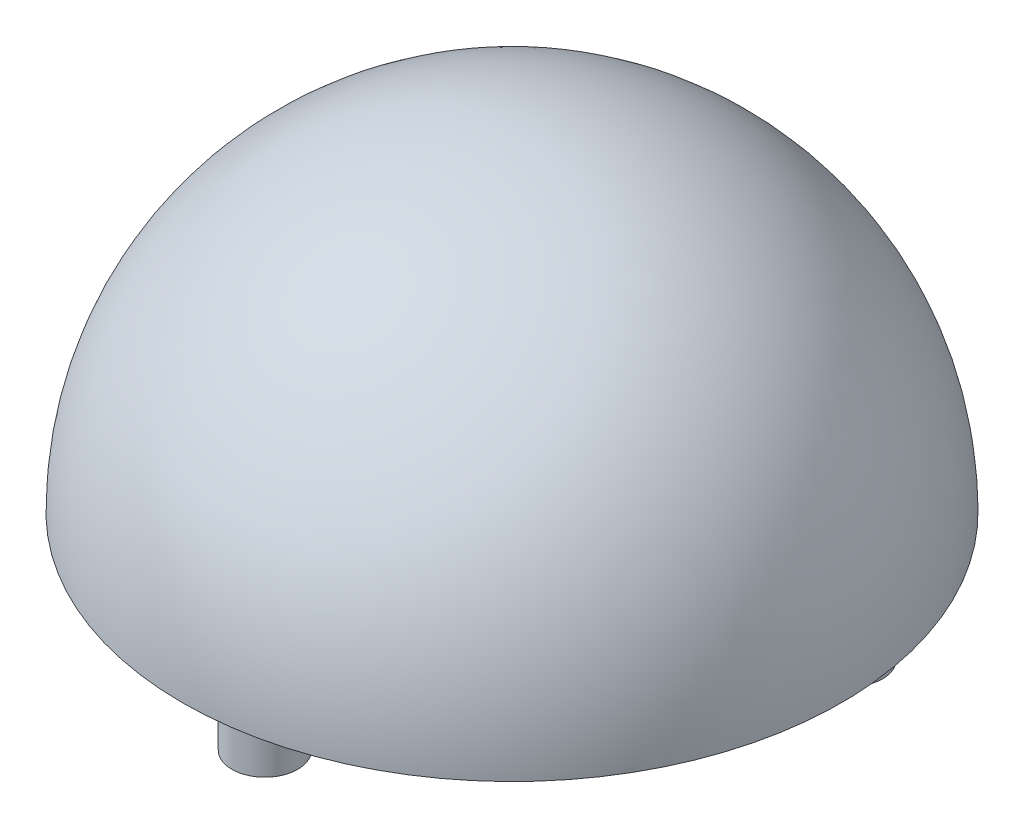
SolidWorks part; units mm, degrees
material "ABS"
ref_plane "Front Plane" through (0, 0, 0) normal (0, 0, 1) x (1, 0, 0)
ref_plane "Top Plane" through (0, 0, 0) normal (0, 1, 0) x (1, 0, 0)
ref_plane "Right Plane" through (0, 0, 0) normal (1, 0, 0) x (0, 0, -1)
sketch "Sketch1" plane through (0, 0, 0) normal (0, 1, 0) x (1, 0, 0)
  line L0 (0, 0) -> (-40, 0)
  line L1 (-40, 0) -> (40, 0)
  arc A0 (40, 0) -> (-40, 0) centre (0, 0) ccw
  dimension "D1" = 80
revolve "Revolve1" add sketch "Sketch1" angle 180 about L1
sketch "Sketch2" plane through (0, 0, 0) normal (0, -1, 0) x (-1, 0, 0)
  line L0 (0, -30) -> (0, 30)
  circle A0 centre (0, 0) radius 30
  circle A1 centre (0, 30) radius 30
  circle A2 centre (0, -30) radius 4
  circle A3 centre (25.9808, 15) radius 4
  circle A4 centre (-25.9808, 15) radius 4
  circle A5 centre (25.9808, 15) radius 1.5
  circle A6 centre (-25.9808, 15) radius 1.5
  circle A7 centre (0, -30) radius 1.5
  dimension "D1" = 60
  dimension "D2" = 8
  dimension "D3" = 8
  dimension "D4" = 8
  dimension "D5" = 3
  dimension "D6" = 3
  dimension "D7" = 3
sketch "Sketch3" plane through (0, 0, 0) normal (0, -1, 0) x (1, 0, 0)
  line L0 (0, 36) -> (0, -36)
  arc A0 (0, -36) -> (0, 36) centre (0, 0) ccw
  dimension "D1" = 72
revolve "Cut-Revolve1" cut sketch "Sketch3" angle 180 about L0
sketch "Sketch4" plane through (0, 0, 0) normal (0, -1, 0) x (1, 0, 0)
  circle A0 centre (0, 0) radius 39
  dimension "D1" = 78
extrude "Boss-Extrude2" add sketch "Sketch4" against normal blind 4
extrude "Boss-Extrude3" add sketch "Sketch2" along normal blind 10 contours A7 A0 A2 | A7 L0 A2 A0 | A7 A0 A2 L0 | A6 A1 A4 A0 | A6 A0 A4 A1 | A6 A1 A4 A0 | A6 A0 A4 A1 | A5 A0 A3 A1 | A5 A1 A3 A0 | A5 A0 A3 A1 | A5 A1 A3 A0
sketch "Sketch5" plane through (0, 0, 0) normal (0, -1, 0) x (1, 0, 0)
  circle A0 centre (0, 0) radius 22.5
  dimension "D1" = 45
extrude "Cut-Extrude1" cut sketch "Sketch5" against normal blind 5
sketch "Sketch6" plane through (0, 0, 0) normal (0, -1, 0) x (1, 0, 0)
  line L1 (-3, 25) -> (3, 25)
  line L2 (-3, 25) -> (-3, -27)
  line L3 (-3, -27) -> (3, -27)
  line L4 (3, 25) -> (3, -27)
  line L5 (-27, 3) -> (27, 3)
  line L6 (-27, 3) -> (-27, -3)
  line L7 (-27, -3) -> (27, -3)
  line L8 (27, 3) -> (27, -3)
  circle M6 centre (0, 0) radius 22.5
  dimension "D1" = 6
  dimension "D2" = 6
  dimension "D3" = 3
  dimension "D4" = 3
  dimension "D5" = 54
  dimension "D6" = 27
  dimension "D7" = 52
  dimension "D8" = 27
extrude "Boss-Extrude4" add sketch "Sketch6" against normal blind 5 contours L6 L7 L5 M6 | L7 L2 L5 M6 | L2 L7 L4 L5 | L4 L7 L5 M6 | L8 L5 L7 M6 | L2 L5 L4 M6 | L4 L1 L2 M6 | L7 L2 L4 M6 | L4 L2 L3 M6
sketch "Sketch7" plane through (0, 0, 0) normal (0, -1, 0) x (1, 0, 0)
  circle A0 centre (0, 0) radius 7
  dimension "D1" = 14
extrude "Boss-Extrude5" add sketch "Sketch7" against normal blind 5
sketch "Sketch8" plane through (0, 0, 0) normal (0, -1, 0) x (1, 0, 0)
  line L1 (-1, 4.3) -> (1, 4.3)
  line L2 (-1, 4.3) -> (-1, -4.3)
  line L3 (-1, -4.3) -> (1, -4.3)
  line L4 (1, 4.3) -> (1, -4.3)
  line L5 (-4.3, 1) -> (4.3, 1)
  line L6 (-4.3, 1) -> (-4.3, -1)
  line L7 (-4.3, -1) -> (4.3, -1)
  line L8 (4.3, 1) -> (4.3, -1)
  circle A0 centre (0, 0) radius 3
  dimension "D1" = 6
  dimension "D2" = 2
  dimension "D3" = 2
  dimension "D4" = 1
  dimension "D5" = 1
  dimension "D6" = 8.6
  dimension "D7" = 4.3
  dimension "D8" = 8.6
  dimension "D9" = 4.3
extrude "Boss-Extrude6" add sketch "Sketch8" along normal blind 10 contours A0 L5 L6 L7 | A0 L4 L1 L2 | L2 A0 L5 | L4 A0 L2 L5 | L5 A0 L4 | L7 A0 L5 L4 | A0 L7 L8 L5 | L2 L7 L4 L5 | L5 A0 L7 L2 | L4 A0 L7 | L7 A0 L2 | L2 A0 L4 L7 | A0 L2 L3 L4
